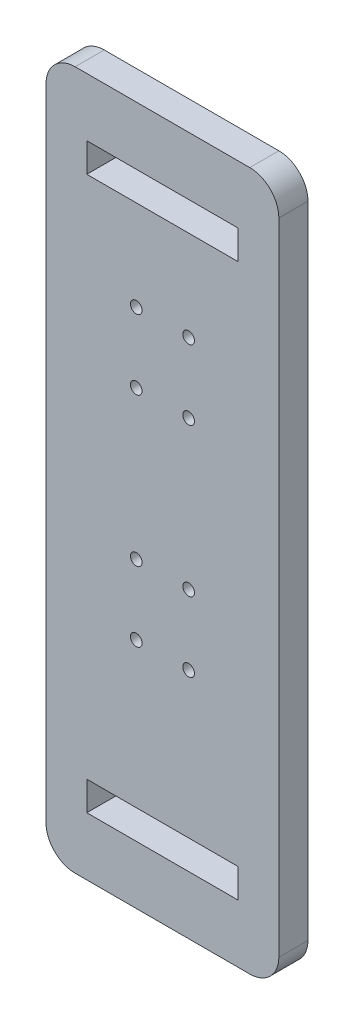
SolidWorks part; units mm, degrees
ref_plane "Front Plane" through (0, 0, 0) normal (0, 0, 1) x (1, 0, 0)
ref_plane "Top Plane" through (0, 0, 0) normal (0, 1, 0) x (1, 0, 0)
ref_plane "Right Plane" through (0, 0, 0) normal (1, 0, 0) x (0, 0, -1)
sketch "Sketch1" plane through (0, 0, 0) normal (0, 0, 1) x (1, 0, 0)
  line L1 (0, 0) -> (-80, 0)
  line L2 (0, 0) -> (0, 240)
  line L3 (0, 240) -> (-80, 240)
  line L4 (-80, 0) -> (-80, 240)
  dimension "D1" = 240
  dimension "D2" = 80
extrude "Boss-Extrude1" add sketch "Sketch1" along normal blind 10
fillet "Fillet2" radius 10 4 edges at (0, 0, 5) (-80, 0, 5) (-80, 240, 5) (0, 240, 5)
sketch "Sketch2" plane through (0, 0, 10) normal (0, 0, 1) x (1, 0, 0)
  line L0 (-80, 120) -> (0, 120) construction
  line L1 (-80, 230) -> (-80, 10) construction
  line L2 (0, 10) -> (0, 230) construction
  line L3 (0, 120) -> (-40, 120) construction
  line L4 (-40, 120) -> (-40, 210) construction
  line L5 (-40, 120) -> (-40, 30) construction
  line L6 (-40, 210) -> (-40, 215) construction
  line L7 (-40, 30) -> (-40, 25) construction
  line L8 (-40, 210) -> (-40, 172.2494) construction
  line L9 (-14, 210) -> (-66, 210)
  line L10 (-14, 210) -> (-14, 220)
  line L11 (-14, 220) -> (-66, 220)
  line L12 (-66, 210) -> (-66, 220)
  line L13 (-14, 210) -> (-66, 220) construction
  line L14 (-14, 220) -> (-66, 210) construction
  line L15 (-14, 20) -> (-66, 20)
  line L16 (-14, 20) -> (-14, 30)
  line L17 (-14, 30) -> (-66, 30)
  line L18 (-66, 20) -> (-66, 30)
  line L19 (-14, 20) -> (-66, 30) construction
  line L20 (-14, 30) -> (-66, 20) construction
  line L21 (-50.6528, 210) -> (-50.6528, 178.94) construction
  line L22 (-40, 178.94) -> (-49, 178.94) construction
  line L23 (-40, 178.94) -> (-31, 178.94) construction
  line L24 (-49, 178.94) -> (-49, 154.94) construction
  line L25 (-31, 178.94) -> (-31, 154.94) construction
  circle A0 centre (-49, 154.94) radius 2
  circle A1 centre (-31, 154.94) radius 2
  circle A2 centre (-31, 178.94) radius 2
  circle A3 centre (-49, 178.94) radius 2
  circle A8 centre (-49, 103.94) radius 2
  circle A9 centre (-49, 79.94) radius 2
  circle A10 centre (-31, 103.94) radius 2
  circle A11 centre (-31, 79.94) radius 2
  dimension "D14" = 4
  dimension "D15" = 4
  dimension "D16" = 4
  dimension "D17" = 4
  dimension "D1" = 90
  dimension "D2" = 90
  dimension "D3" = 5
  dimension "D4" = 5
  dimension "D5" = 10
  dimension "D6" = 52
  dimension "D7" = 52
  dimension "D8" = 10
  dimension "D9" = 31.06
  dimension "D10" = 9
  dimension "D11" = 9
  dimension "D12" = 24
  dimension "D13" = 24
  dimension "D18" = 2
extrude "Cut-Extrude1" cut sketch "Sketch2" against normal blind 10
